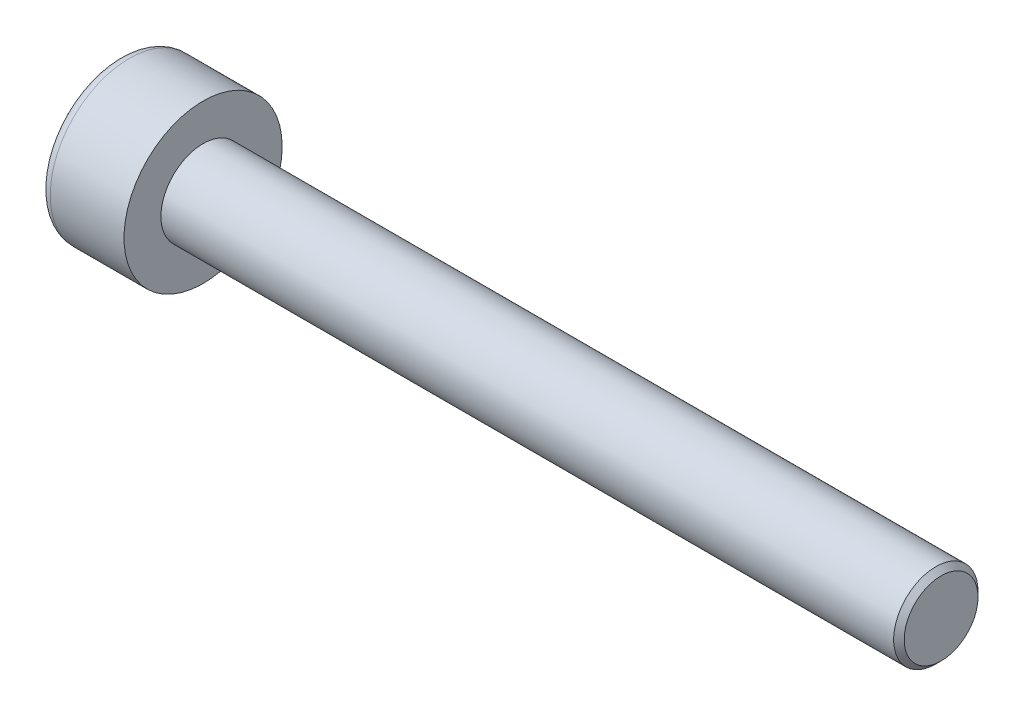
SolidWorks part; units mm, degrees
ref_plane "Front" through (0, 0, 0) normal (0, 0, 1) x (1, 0, 0)
ref_plane "Top" through (0, 0, 0) normal (0, 1, 0) x (1, 0, 0)
ref_plane "Right" through (0, 0, 0) normal (1, 0, 0) x (0, 0, -1)
sketch "Sketch1" plane through (0, 0, 0) normal (1, 0, 0) x (0, 0, -1)
  circle A0 centre (0, 0) radius 1.5
  dimension "dk" = 3
extrude "BaseHead" add sketch "Sketch1" along normal blind 1.6
sketch "Sketch2" plane through (1.6, 0, 0) normal (1, 0, 0) x (0, 0, -1)
  circle A0 centre (0, 0) radius 0.8
  dimension "d" = 1.6
extrude "BaseBody" add sketch "Sketch2" along normal blind 14
cosmetic thread "ThreadCosmetic1" parameters "b"=16, "D2"=1.221
sketch "Sketch3" plane through (0, 0, 0) normal (1, 0, 0) x (0, 0, -1)
  line L1 (0.866, 0) -> (0.433, 0.75)
  line L2 (0.433, 0.75) -> (-0.433, 0.75)
  line L3 (-0.433, 0.75) -> (-0.866, 0)
  line L4 (-0.866, 0) -> (-0.433, -0.75)
  line L5 (-0.433, -0.75) -> (0.433, -0.75)
  line L6 (0.433, -0.75) -> (0.866, 0)
  circle A0 centre (0, 0) radius 0.75 construction
  dimension "s" = 1.5
  dimension "e" = 1.7321
extrude "HexagonSocket" cut sketch "Sketch3" along normal blind 0.7
sketch "Sketch4" plane through (-4.1961, 0.75, 0) normal (0, 0, 1) x (-1, 0, 0)
  line L0 (-4.8961, 1.5) -> (-5.3292, 0.75)
  line L2 (-5.3292, 0.75) -> (-4.8961, 0.75)
  line L3 (-4.8961, 0.75) -> (-4.8961, 1.5)
  line L4 (-5.0351, 0.75) -> (0.839, 0.75) construction
  line L5 (-19.7961, 0.75) -> (-5.7961, 0.75) construction
  line L6 (-5.7961, 0.75) -> (-4.1961, 0.75) construction
  dimension "m" = 60
revolve "Cut-Revolve1" cut sketch "Sketch4" angle 360 about L4
fillet "HeadFillet" [suppressed] radius 0.1
fillet "TopFillet" radius 0.2 1 edges at (0, 0, -1.5)
chamfer "Chamfer1" distance 0.1 angle 45 1 edges at (15.6, 0, -0.8)
sketch "Sketch5" plane through (0, 0, 0) normal (0, 0, 1) x (1, 0, 0)
  line L0 (15.5, 0.6359) -> (15.5947, 0.8)
  line L1 (15.5947, 0.8) -> (15.5947, 0.9895)
  line L2 (15.5947, 0.9895) -> (15.4052, 0.9895)
  line L3 (15.4052, 0.9895) -> (15.4052, 0.8)
  line L4 (15.4052, 0.8) -> (15.5, 0.6359)
  line L5 (0, 0) -> (7.8886, 0) construction
  line L6 (15.5, -0.8) -> (15.5, 0.8) construction
  dimension "D1" = 1.6
  dimension "D2" = 0.1895
revolve "Cut-Revolve10" [suppressed] cut sketch "Sketch5" angle 360 about L5
pattern_linear "LPattern10" [suppressed] count 70 spacing 0.2274 along (1, 0, 0)
equation "\"r1@TopFillet\" = \"d@Sketch2\" / 8"
equation "\"D1@Chamfer1\" = \"r@HeadFillet\""
equation "\"D1@Sketch5\" = \"d@Sketch2\""
equation "\"D2@Sketch5\" =  ( \"d@Sketch2\" - \"D2@ThreadCosmetic1\" )  / 2"
equation "\"D3@LPattern10\" = \"D2@Sketch5\" * 1.2"
equation "\"D1@LPattern10\" = \"b@ThreadCosmetic1\" / \"D3@LPattern10\""
